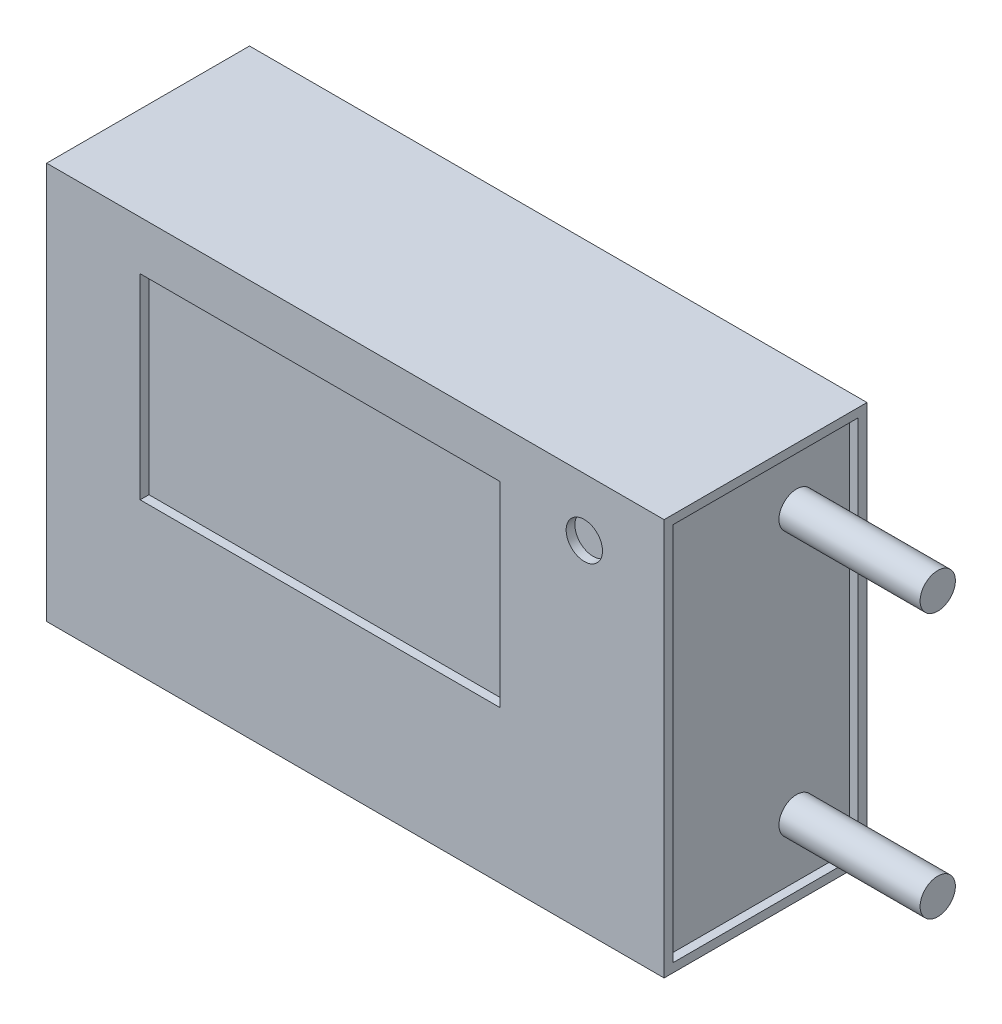
SolidWorks part; units mm, degrees
ref_plane "Front Plane" through (0, 0, 0) normal (0, 0, 1) x (1, 0, 0)
ref_plane "Top Plane" through (0, 0, 0) normal (0, 1, 0) x (1, 0, 0)
ref_plane "Right Plane" through (0, 0, 0) normal (1, 0, 0) x (0, 0, -1)
sketch "Sketch1" plane through (0, 0, 0) normal (0, 0, 1) x (1, 0, 0)
  line L1 (-21, 11.25) -> (21, 11.25)
  line L2 (-21, 11.25) -> (-21, -11.25)
  line L3 (-21, -11.25) -> (21, -11.25)
  line L4 (21, 11.25) -> (21, -11.25)
  point P4 (0, 11.25)
  point P6 (21, 0)
  dimension "D1" = 42
  dimension "D2" = 22.5
extrude "Boss-Extrude1" add sketch "Sketch1" along normal mid plane 11.5
sketch "Sketch2" plane through (21, 0, 0) normal (1, 0, 0) x (0, 0, -1)
  line L8 (5.25, -10.75) -> (5.25, 10.75)
  line L9 (5.25, 10.75) -> (-5.25, 10.75)
  line L10 (-5.25, 10.75) -> (-5.25, -10.75)
  line L11 (-5.25, -10.75) -> (5.25, -10.75)
  line L12 (5.25, -10.75) -> (5.25, 10.75)
  line L13 (5.25, 10.75) -> (-5.25, 10.75)
  line L14 (-5.25, 10.75) -> (-5.25, -10.75)
  line L15 (-5.25, -10.75) -> (5.25, -10.75)
  dimension "D1" = 0.5
extrude "Cut-Extrude1" cut sketch "Sketch2" against normal blind 4
mirror "Mirror1" about plane through (0, 0, 0) normal (1, 0, 0) of "Cut-Extrude1"
sketch "Sketch7" plane through (0, 0, -5.75) normal (0, 0, 1) x (1, 0, 0)
  line L13 (0, 0) -> (0, 14.5362) construction
  line L14 (24.1679, -4.1306) -> (21, -4.1306)
  line L15 (24.1679, -14.1807) -> (24.1679, -4.1306)
  line L16 (17, -14.1807) -> (24.1679, -14.1807)
  line L17 (17, -11.25) -> (17, -14.1807)
  line L18 (21, -4.1306) -> (17, -11.25)
  line L19 (-18.8, 11.25) -> (-21, 11.25) construction
  line L20 (-21, 11.25) -> (-21, -11.25) construction
  line L21 (-18.8, -11.25) -> (-21, -11.25) construction
  line L22 (-18.8, 11.25) -> (-18.8, -11.25) construction
  line L23 (17, -10.75) -> (17, 10.75) construction
  line L24 (21, -11.25) -> (21, 11.25) construction
  line L25 (-21, -11.25) -> (21, -11.25) construction
extrude "Cut-Extrude3" [suppressed] cut sketch "Sketch7" along normal through all
sketch "Sketch8" plane through (0, 0, 5.75) normal (0, 0, 1) x (1, 0, 0)
  line L4 (-21, 11.25) -> (-18.8, 11.25)
  line L5 (-18.8, 11.25) -> (-18.8, -11.25)
  line L6 (-21, -11.25) -> (-18.8, -11.25)
  line L7 (-21, 11.25) -> (-21, -11.25)
extrude "Cut-Extrude4" [suppressed] cut sketch "Sketch8" against normal through all
sketch "Sketch3" plane through (17, 0, 0) normal (1, 0, 0) x (0, 0, -1)
  line L0 (0, 0) -> (14.9659, 0) construction
  circle A0 centre (2.2599, 7.5) radius 1
  circle A1 centre (2.2599, -7.5) radius 1
  dimension "D1" = 15
  dimension "D2" = 2
extrude "Boss-Extrude2" add sketch "Sketch3" along normal blind 8
sketch "Sketch4" plane through (-17, 0, 0) normal (-1, 0, 0) x (0, 0, 1)
  line L0 (0, 0) -> (-8.186, 0) construction
  circle A0 centre (-3.3648, 2.9881) radius 0.5
  circle A1 centre (-3.3648, -2.9881) radius 0.5
  dimension "D1" = 1
extrude "Boss-Extrude3" add sketch "Sketch4" along normal blind 8
sketch "Sketch5" plane through (0, 0, 5.75) normal (0, 0, 1) x (1, 0, 0)
  line L1 (-12.1998, 8.4726) -> (8.1922, 8.4726)
  line L2 (-12.1998, 8.4726) -> (-12.1998, -2.6263)
  line L3 (-12.1998, -2.6263) -> (8.1922, -2.6263)
  line L4 (8.1922, 8.4726) -> (8.1922, -2.6263)
  circle A0 centre (12.9768, 7.9646) radius 1.0306
extrude "Cut-Extrude2" cut sketch "Sketch5" against normal blind 0.5
sketch "Sketch6" plane through (0, 0, -5.75) normal (0, 0, -1) x (-1, 0, 0)
  line L0 (23.548, 0) -> (0, 0)
  line L2 (0, 0) -> (0, -11.25)
sketch "Sketch9" plane through (21, 0, 0) normal (1, 0, 0) x (0, 0, -1)
  line L4 (5.75, -11.25) -> (5.75, 11.25)
  line L5 (5.75, 11.25) -> (-5.75, 11.25)
  line L6 (-5.75, 11.25) -> (-5.75, -11.25)
  line L7 (-5.75, -11.25) -> (5.75, -11.25)
  line L8 (5.75, -11.25) -> (5.75, 11.25)
  line L9 (5.75, 11.25) -> (-5.75, 11.25)
  line L10 (-5.75, 11.25) -> (-5.75, -11.25)
  line L11 (-5.75, -11.25) -> (5.75, -11.25)
  line L13 (5.25, -10.75) -> (5.25, 10.75)
  line L14 (-5.25, -10.75) -> (5.25, -10.75)
  line L15 (-5.25, 10.75) -> (-5.25, -10.75)
  line L16 (5.25, 10.75) -> (-5.25, 10.75)
  line L17 (5.25, -10.75) -> (5.25, 10.75)
  line L18 (-5.25, -10.75) -> (5.25, -10.75)
  line L19 (-5.25, 10.75) -> (-5.25, -10.75)
  line L20 (5.25, 10.75) -> (-5.25, 10.75)
  dimension "D1" = 0
  dimension "D2" = 0
extrude "Cut-Extrude5" cut sketch "Sketch9" against normal offset from surface (3.5 mm away) 0.5 up to face at (17, -7.5, -1.2599)
sketch "Sketch10" plane through (-21, 0, 0) normal (-1, 0, 0) x (0, 0, 1)
  line L4 (-5.75, 11.25) -> (-5.75, -11.25)
  line L5 (-5.75, -11.25) -> (5.75, -11.25)
  line L6 (5.75, -11.25) -> (5.75, 11.25)
  line L7 (5.75, 11.25) -> (-5.75, 11.25)
  line L8 (-5.75, 11.25) -> (-5.75, -11.25)
  line L9 (-5.75, -11.25) -> (5.75, -11.25)
  line L10 (5.75, -11.25) -> (5.75, 11.25)
  line L11 (5.75, 11.25) -> (-5.75, 11.25)
  line L13 (-5.25, -10.75) -> (5.25, -10.75)
  line L14 (-5.25, 10.75) -> (-5.25, -10.75)
  line L15 (5.25, 10.75) -> (-5.25, 10.75)
  line L16 (5.25, -10.75) -> (5.25, 10.75)
  line L17 (-5.25, -10.75) -> (5.25, -10.75)
  line L18 (-5.25, 10.75) -> (-5.25, -10.75)
  line L19 (5.25, 10.75) -> (-5.25, 10.75)
  line L20 (5.25, -10.75) -> (5.25, 10.75)
  dimension "D1" = 0
  dimension "D2" = 0
extrude "Cut-Extrude6" cut sketch "Sketch10" against normal offset from surface (3.5 mm away) 0.5 up to face at (-17, -2.9881, -3.8648)
sketch3d "3DSketch1"
  line L0 (-17.5, 11.25, -5.75) -> (-17.5, 11.25, 5.75)
  line L1 (-17.5, -11.25, 5.75) -> (-17.5, -11.25, -5.75)
  line L2 (17.5, -11.25, 5.75) -> (17.5, -11.25, -5.75)
  line L3 (17.5, 11.25, -5.75) -> (17.5, 11.25, 5.75)
  line L4 (17.5, 11.25, 5.75) -> (-17.5, 11.25, 5.75)
  line L5 (-17.5, 11.25, 5.75) -> (-17.5, -11.25, 5.75)
  line L6 (-17.5, -11.25, 5.75) -> (17.5, -11.25, 5.75)
  line L7 (17.5, -11.25, 5.75) -> (17.5, 11.25, 5.75)
  line L8 (17.5, 11.25, 5.75) -> (-17.5, 11.25, 5.75)
  line L9 (-17.5, 11.25, 5.75) -> (-17.5, -11.25, 5.75)
  line L10 (-17.5, -11.25, 5.75) -> (17.5, -11.25, 5.75)
  line L11 (17.5, -11.25, 5.75) -> (17.5, 11.25, 5.75)
  line L12 (-17.5, -11.25, -5.75) -> (-17.5, 11.25, -5.75)
  line L13 (-17.5, 11.25, -5.75) -> (17.5, 11.25, -5.75)
  line L14 (17.5, 11.25, -5.75) -> (17.5, -11.25, -5.75)
  line L15 (17.5, -11.25, -5.75) -> (-17.5, -11.25, -5.75)
  line L16 (-17.5, -11.25, -5.75) -> (-17.5, 11.25, -5.75)
  line L17 (-17.5, 11.25, -5.75) -> (17.5, 11.25, -5.75)
  line L18 (17.5, 11.25, -5.75) -> (17.5, -11.25, -5.75)
  line L19 (17.5, -11.25, -5.75) -> (-17.5, -11.25, -5.75)
  dimension "D1" = 0
  dimension "D2" = 0
